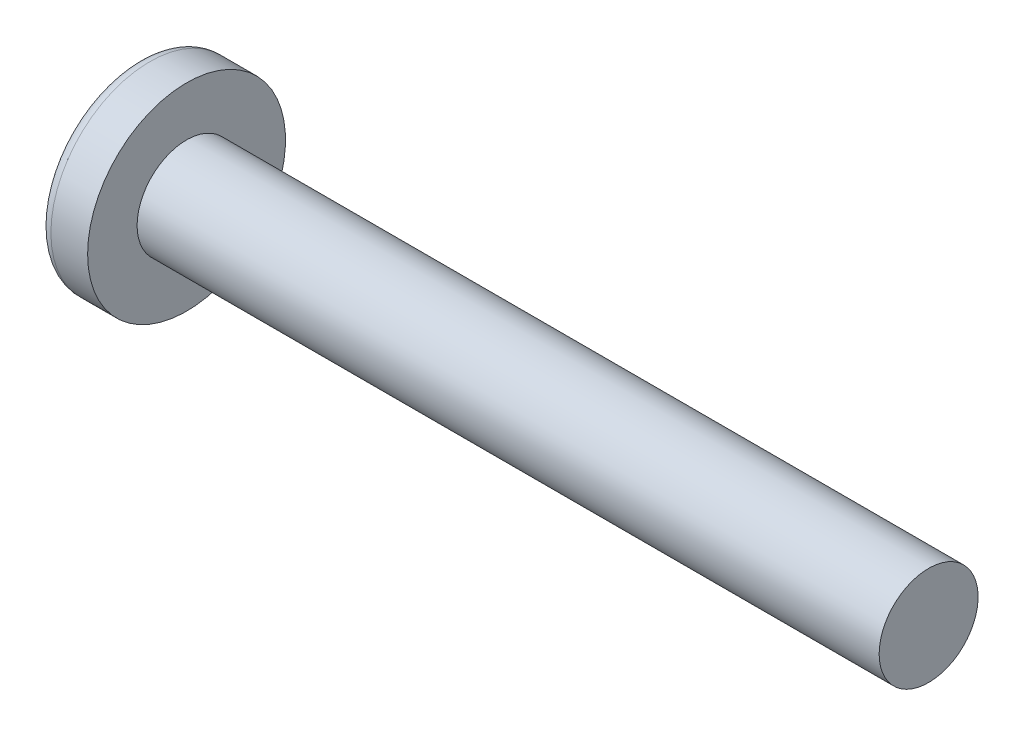
SolidWorks part; units mm, degrees
ref_plane "Plane1" through (0, 0, 0) normal (0, 0, 1) x (1, 0, 0)
ref_plane "Plane2" through (0, 0, 0) normal (0, 1, 0) x (1, 0, 0)
ref_plane "Plane3" through (0, 0, 0) normal (1, 0, 0) x (0, 0, -1)
sketch "BodySke" plane through (0, 0, 0) normal (0, 0, 1) x (1, 0, 0)
  line L0 (3.1, 2) -> (3.1, 4)
  line L1 (3.8, 6.35) -> (3.8, -3.175) construction
  line L2 (-25.4, 0) -> (127, 0) construction
  line L3 (33.1, 0) -> (0, 0)
  line L4 (3.1, 2) -> (33.1, 2)
  line L5 (33.1, 2) -> (33.1, 0)
  line L6 (1.6164, 4) -> (3.1, 4)
  line L7 (3.1, -2) -> (33.1, -2) construction
  line L8 (3.1, 6.35) -> (3.1, -3.175) construction
  arc A0 (1.227, 3.8007) -> (0, 0) centre (6.5, 0) ccw
  arc A2 (1.227, 3.8007) -> (1.6164, 4) centre (1.6164, 3.52) cw
  dimension "Head_fillet_rad" = 0.48
  dimension "Head_crown_rad" = 6.5
  dimension "Head_ht" = 3.1
  dimension "Diameter" = 4
  dimension "Length" = 30
  dimension "Head_dia" = 8
  dimension "Advance" = 0.7
  dimension "Thread_nom" = 30
revolve "Base-Revolve" add sketch "BodySke" angle 360 about L2
cosmetic thread "ThreadCosmetic" [suppressed] parameters "Thread_length"=29.3, "Thread_minor"=3.22
sketch "Sketch3" plane through (0, 0, 0) normal (1, 0, 0) x (0, 0, -1)
  line L0 (0.465, -2.2) -> (-0.465, -2.2)
  line L1 (0.465, -2.2) -> (0.465, 2.2)
  line L2 (-0.465, 2.2) -> (0.465, 2.2)
  line L3 (-0.465, 2.2) -> (-0.465, -2.2)
  dimension "D1" = 2.2
  dimension "Cross_dia" = 4.4
  dimension "D2" = 0.465
  dimension "Cross_width" = 0.93
ref_plane "Plane4" through (2.45, 0, 0) normal (1, 0, 0) x (0, 0, -1)
sketch "Sketch4" plane through (2.45, 0, 0) normal (1, 0, 0) x (0, 0, -1)
  line L0 (0.2325, -0.2325) -> (-0.2325, -0.2325)
  line L1 (0.2325, -0.2325) -> (0.2325, 0.2325)
  line L2 (-0.2325, 0.2325) -> (0.2325, 0.2325)
  line L3 (-0.2325, 0.2325) -> (-0.2325, -0.2325)
  dimension "D1" = 0.465
  dimension "D2" = 0.465
  dimension "D3" = 0.2325
  dimension "D4" = 0.2325
loft "Cut-Loft1" cut profiles "Sketch3", "Sketch4"
pattern_circular "CirPattern1" count 2 every 90 about axis through (0, 0, 0) along (1, 0, 0) of "Cut-Loft1"
sketch "ThdSchSke" plane through (0, 0, 0) normal (0, 0, 1) x (1, 0, 0)
  line L0 (3.8, -1.61) -> (3.5269, -2)
  line L1 (3.8, -1.61) -> (4.0731, -2)
  line L2 (4.0731, -2) -> (4.0731, -2.5)
  line L3 (-3.175, 0) -> (5.1513, 0) construction
  line L5 (4.0731, -2.5) -> (3.5269, -2.5)
  line L6 (3.5269, -2.5) -> (3.5269, -2)
  dimension "Thread_minor" = 3.22
  dimension "Diameter" = 4
  dimension "Start" = 3.8
  dimension "SideAngle" = 55
  dimension "VeeAngle" = 70
  dimension "Overcut" = 5
revolve "ThreadSchematic" [suppressed] cut sketch "ThdSchSke" angle 360 about L3
pattern_linear "ThdSchPat" [suppressed]
equation "\"D1@Sketch3\" = \"Cross_dia@Sketch3\" / 2"
equation "\"D2@Sketch3\" = \"Cross_width@Sketch3\" / 2"
equation "\"D1@Sketch4\" = \"Cross_width@Sketch3\" *.5"
equation "\"D2@Sketch4\" = \"D1@Sketch4\""
equation "\"D3@Sketch4\" = \"D1@Sketch4\" / 2"
equation "\"D4@Sketch4\" = \"D2@Sketch4\" / 2"
equation "\"Thread_length@ThreadCosmetic\" = ((sgn( (\"Length@BodySke\" - \"Advance@BodySke\" ) - \"Thread_nom@BodySke\" )-1)*( (\"Length@BodySke\" - \"Advance@BodySke\" ) - \"Thread_nom@BodySke\" ))/-2+ \"Thread_nom@BodySke\""
equation "\"Thread_minor@ThdSchSke\" = \"Thread_minor@ThreadCosmetic\""
equation "\"Diameter@ThdSchSke\" = \"Diameter@BodySke\""
equation "\"Overcut@ThdSchSke\" = \"Diameter@BodySke\" * 1.25"
equation "\"Start@ThdSchSke\" = \"Head_ht@BodySke\" + \"Length@BodySke\" - \"Thread_length@ThreadCosmetic\"  '---Non-countersunk---"
equation "\"Num_threads@ThdSchPat\" = int( \"Thread_length@ThreadCosmetic\" / \"Advance@BodySke\" + 0.999 )  + 1"
equation "\"Advance@ThdSchPat\" = \"Thread_length@ThreadCosmetic\" /  (\"Num_threads@ThdSchPat\" - 1) 'relax it"
